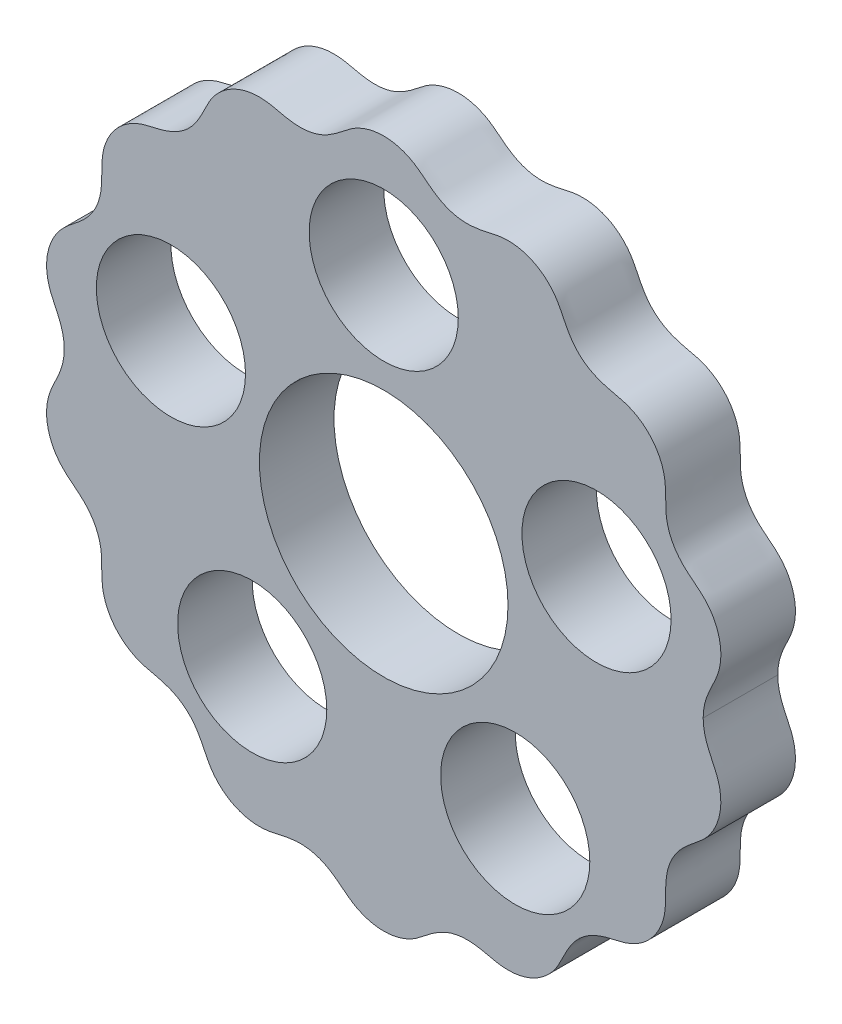
SolidWorks part; units mm, degrees
ref_plane "前视基准面" through (0, 0, 0) normal (0, 0, 1) x (1, 0, 0)
ref_plane "上视基准面" through (0, 0, 0) normal (0, 1, 0) x (1, 0, 0)
ref_plane "右视基准面" through (0, 0, 0) normal (1, 0, 0) x (0, 0, -1)
sketch "草图1" plane through (0, 0, 0) normal (0, 0, 1) x (1, 0, 0)
  line L0 (0, 0) -> (19.2125, 0) construction
  line L1 (19.2125, 0) -> (0, 0) construction
  line L2 (-13.0001, 0) -> (-15.8633, 0) construction
  spline S0 degree 4 poles (11.5135, 6.3336) (11.527, 6.2231) (11.5668, 6.0038) (11.6783, 5.6586) (11.9398, 5.2291) (12.3169, 4.8533) (12.7144, 4.5714) (13.0267, 4.2874) (13.2395, 4.0257) (13.3758, 3.817) (13.483, 3.611) (13.5552, 3.4371) (13.6059, 3.284) (13.6447, 3.1396) (13.6735, 3.0054) (13.6932, 2.8739) (13.7052, 2.751) (13.7102, 2.6455) (13.7111, 2.5545) (13.7091, 2.4602) (13.7056, 2.4011) (13.6985, 2.3206) (13.6885, 2.2338) (13.6763, 2.1514) (13.6589, 2.0606) (13.6342, 1.9553) (13.6051, 1.8508) (13.5717, 1.748) (13.517, 1.5994) (13.4338, 1.4076) (13.3178, 1.1764) (13.1849, 0.8966) (13.0721, 0.5847) (12.9994, 0.2368) (12.988, -0.1793) (13.0767, -0.6516) (13.2789, -1.1115) (13.526, -1.5754) (13.7034, -2.1387) (13.7437, -2.788) (13.6035, -3.4164) (13.3056, -3.968) (12.9261, -4.3975) (12.5717, -4.6706) (12.2507, -4.9214) (11.9118, -5.2776) (11.6864, -5.6334) (11.5501, -6.0331) (11.4958, -6.4466) (11.4872, -6.741) (11.4935, -7.0742) (11.4831, -7.4477) (11.3954, -7.9388) (11.1486, -8.5104) (10.7515, -9.0022) (10.2357, -9.3664) (9.7027, -9.5815) (9.1958, -9.6812) (8.6166, -9.8223) (8.0718, -10.1348) (7.6495, -10.5997) (7.3862, -11.1344) (7.1745, -11.6057) (6.843, -12.0753) (6.3712, -12.4934) (5.7973, -12.7698) (5.1733, -12.8799) (4.6659, -12.8482) (4.2925, -12.7678) (3.8977, -12.671) (3.4202, -12.5933) (2.9279, -12.6301) (2.4661, -12.8002) (2.1107, -13.0186) (1.8754, -13.1972) (1.6194, -13.4097) (1.3216, -13.6307) (0.885, -13.8635) (0.2879, -14.0232) (-0.3414, -14.0176) (-0.9463, -13.8403) (-1.4461, -13.5566) (-1.8397, -13.2219) (-2.312, -12.858) (-2.8966, -12.6285) (-3.5234, -12.5899) (-4.1054, -12.7185) (-4.6059, -12.8462) (-5.1801, -12.8785) (-5.7997, -12.769) (-6.3719, -12.4926) (-6.8429, -12.0754) (-7.1745, -11.6056) (-7.3862, -11.1344) (-7.6495, -10.5997) (-8.0718, -10.1348) (-8.6166, -9.8224) (-9.1958, -9.6811) (-9.7027, -9.5816) (-10.2356, -9.3663) (-10.6857, -9.0488) (-11.0496, -8.6352) (-11.2927, -8.1828) (-11.4194, -7.7999) (-11.4803, -7.4348) (-11.4944, -7.0969) (-11.4854, -6.7168) (-11.5007, -6.2924) (-11.604, -5.8312) (-11.8377, -5.3687) (-12.1451, -5.0141) (-12.4683, -4.7498) (-12.7596, -4.5257) (-12.997, -4.3126) (-13.2302, -4.0471) (-13.4408, -3.7207) (-13.641, -3.2535) (-13.7387, -2.7051) (-13.7032, -2.1387) (-13.526, -1.5754) (-13.2789, -1.1115) (-13.0767, -0.6516) (-12.988, -0.1793) (-12.9994, 0.2368) (-13.072, 0.5848) (-13.1849, 0.8966) (-13.3178, 1.1764) (-13.4338, 1.4076) (-13.517, 1.5994) (-13.5717, 1.748) (-13.6051, 1.8508) (-13.6342, 1.9553) (-13.6589, 2.0606) (-13.6763, 2.1514) (-13.6885, 2.2338) (-13.6985, 2.3206) (-13.7056, 2.4011) (-13.7091, 2.4602) (-13.7111, 2.5545) (-13.7102, 2.6455) (-13.7052, 2.751) (-13.6932, 2.8739) (-13.6735, 3.0054) (-13.6447, 3.1396) (-13.6059, 3.284) (-13.5552, 3.4371) (-13.483, 3.611) (-13.3758, 3.817) (-13.2395, 4.0257) (-13.0267, 4.2874) (-12.7144, 4.5714) (-12.3169, 4.8533) (-11.9398, 5.2291) (-11.6783, 5.6586) (-11.5668, 6.0038) (-11.527, 6.2231) (-11.5135, 6.3336) knots 0 0 0 0 0 0.007437 0.014874 0.024076 0.033277 0.042729 0.047455 0.052181 0.055773 0.059366 0.062958 0.064755 0.066551 0.069353 0.072156 0.073557 0.074958 0.076359 0.077761 0.079568 0.080471 0.081375 0.083182 0.08499 0.086797 0.088604 0.090412 0.092219 0.097388 0.102556 0.107725 0.112894 0.11954 0.126185 0.135429 0.144674 0.152994 0.161315 0.174598 0.187704 0.195264 0.202824 0.212649 0.217562 0.222474 0.235597 0.240509 0.245422 0.250335 0.255248 0.262808 0.270368 0.283474 0.29646 0.304321 0.312183 0.321594 0.331004 0.344001 0.353412 0.362824 0.370685 0.378547 0.391533 0.404567 0.412523 0.420479 0.425284 0.430089 0.439698 0.452744 0.457676 0.462607 0.467539 0.47247 0.479922 0.487374 0.500409 0.513394 0.521256 0.529118 0.538528 0.547939 0.560935 0.570347 0.579758 0.58762 0.595482 0.608467 0.621453 0.629315 0.637176 0.646588 0.655999 0.668996 0.678406 0.687817 0.695679 0.70354 0.716526 0.724297 0.732069 0.737708 0.743347 0.748986 0.754625 0.763148 0.771671 0.78029 0.788909 0.794231 0.799552 0.804873 0.810195 0.817798 0.825402 0.838685 0.847006 0.855326 0.864571 0.873815 0.88046 0.887106 0.892275 0.897444 0.902612 0.907781 0.909588 0.911396 0.913203 0.91501 0.916818 0.918625 0.919529 0.920432 0.922239 0.923641 0.925042 0.926443 0.927844 0.930647 0.933449 0.935245 0.937042 0.940634 0.944227 0.947819 0.952545 0.957271 0.966723 0.975924 0.985126 0.992563 1 1 1 1 1 construction
  spline S1 degree 4 poles (13.0001, 0) (13.0001, -0.0846) (13.0122, -0.3074) (13.0826, -0.6652) (13.2789, -1.1115) (13.526, -1.5754) (13.7034, -2.1387) (13.7437, -2.788) (13.6035, -3.4164) (13.3056, -3.968) (12.9261, -4.3975) (12.5717, -4.6706) (12.2507, -4.9214) (11.9118, -5.2776) (11.6864, -5.6334) (11.5501, -6.0331) (11.4958, -6.4466) (11.4872, -6.741) (11.4935, -7.0742) (11.4831, -7.4477) (11.3954, -7.9388) (11.1486, -8.5104) (10.7515, -9.0022) (10.2357, -9.3664) (9.7027, -9.5815) (9.1958, -9.6812) (8.6166, -9.8223) (8.0718, -10.1348) (7.6495, -10.5997) (7.3862, -11.1344) (7.1745, -11.6057) (6.843, -12.0753) (6.3712, -12.4934) (5.7973, -12.7698) (5.1733, -12.8799) (4.6659, -12.8482) (4.2925, -12.7678) (3.8977, -12.671) (3.4202, -12.5933) (2.9279, -12.6301) (2.4661, -12.8002) (2.1107, -13.0186) (1.8754, -13.1972) (1.6194, -13.4097) (1.3216, -13.6307) (0.885, -13.8635) (0.2879, -14.0232) (-0.3414, -14.0176) (-0.9463, -13.8403) (-1.4461, -13.5566) (-1.8397, -13.2219) (-2.312, -12.858) (-2.8966, -12.6285) (-3.5234, -12.5899) (-4.1054, -12.7185) (-4.6059, -12.8462) (-5.1801, -12.8785) (-5.7997, -12.769) (-6.3719, -12.4926) (-6.8429, -12.0754) (-7.1745, -11.6056) (-7.3862, -11.1344) (-7.6495, -10.5997) (-8.0718, -10.1348) (-8.6166, -9.8224) (-9.1958, -9.6811) (-9.7027, -9.5816) (-10.2356, -9.3663) (-10.6857, -9.0488) (-11.0496, -8.6352) (-11.2927, -8.1828) (-11.4194, -7.7999) (-11.4803, -7.4348) (-11.4944, -7.0969) (-11.4854, -6.7168) (-11.5007, -6.2924) (-11.604, -5.8312) (-11.8377, -5.3687) (-12.1451, -5.0141) (-12.4683, -4.7498) (-12.7596, -4.5257) (-12.997, -4.3126) (-13.2302, -4.0471) (-13.4408, -3.7207) (-13.641, -3.2535) (-13.7387, -2.7051) (-13.7032, -2.1387) (-13.526, -1.5754) (-13.2789, -1.1115) (-13.0827, -0.6652) (-13.0122, -0.3074) (-13.0001, -0.0846) (-13.0001, 0) knots 0.120529 0.120529 0.120529 0.120529 0.120529 0.126185 0.135429 0.144674 0.152994 0.161315 0.174598 0.187704 0.195264 0.202824 0.212649 0.217562 0.222474 0.235597 0.240509 0.245422 0.250335 0.255248 0.262808 0.270368 0.283474 0.29646 0.304321 0.312183 0.321594 0.331004 0.344001 0.353412 0.362824 0.370685 0.378547 0.391533 0.404567 0.412523 0.420479 0.425284 0.430089 0.439698 0.452744 0.457676 0.462607 0.467539 0.47247 0.479922 0.487374 0.500409 0.513394 0.521256 0.529118 0.538528 0.547939 0.560935 0.570347 0.579758 0.58762 0.595482 0.608467 0.621453 0.629315 0.637176 0.646588 0.655999 0.668996 0.678406 0.687817 0.695679 0.70354 0.716526 0.724297 0.732069 0.737708 0.743347 0.748986 0.754625 0.763148 0.771671 0.78029 0.788909 0.794231 0.799552 0.804873 0.810195 0.817798 0.825402 0.838685 0.847006 0.855326 0.864571 0.873815 0.879471 0.879471 0.879471 0.879471 0.879471
  spline S2 degree 4 poles (13.0001, 0) (13.0001, 0.0846) (13.0122, 0.3074) (13.0826, 0.6652) (13.2789, 1.1115) (13.526, 1.5754) (13.7034, 2.1387) (13.7437, 2.788) (13.6035, 3.4164) (13.3056, 3.968) (12.9261, 4.3975) (12.5717, 4.6706) (12.2507, 4.9214) (11.9118, 5.2776) (11.6864, 5.6334) (11.5501, 6.0331) (11.4958, 6.4466) (11.4872, 6.741) (11.4935, 7.0742) (11.4831, 7.4477) (11.3954, 7.9388) (11.1486, 8.5104) (10.7515, 9.0022) (10.2357, 9.3664) (9.7027, 9.5815) (9.1958, 9.6812) (8.6166, 9.8223) (8.0718, 10.1348) (7.6495, 10.5997) (7.3862, 11.1344) (7.1745, 11.6057) (6.843, 12.0753) (6.3712, 12.4934) (5.7973, 12.7698) (5.1733, 12.8799) (4.6659, 12.8482) (4.2925, 12.7678) (3.8977, 12.671) (3.4202, 12.5933) (2.9279, 12.6301) (2.4661, 12.8002) (2.1107, 13.0186) (1.8754, 13.1972) (1.6194, 13.4097) (1.3216, 13.6307) (0.885, 13.8635) (0.2879, 14.0232) (-0.3414, 14.0176) (-0.9463, 13.8403) (-1.4461, 13.5566) (-1.8397, 13.2219) (-2.312, 12.858) (-2.8966, 12.6285) (-3.5234, 12.5899) (-4.1054, 12.7185) (-4.6059, 12.8462) (-5.1801, 12.8785) (-5.7997, 12.769) (-6.3719, 12.4926) (-6.8429, 12.0754) (-7.1745, 11.6056) (-7.3862, 11.1344) (-7.6495, 10.5997) (-8.0718, 10.1348) (-8.6166, 9.8224) (-9.1958, 9.6811) (-9.7027, 9.5816) (-10.2356, 9.3663) (-10.6857, 9.0488) (-11.0496, 8.6352) (-11.2927, 8.1828) (-11.4194, 7.7999) (-11.4803, 7.4348) (-11.4944, 7.0969) (-11.4854, 6.7168) (-11.5007, 6.2924) (-11.604, 5.8312) (-11.8377, 5.3687) (-12.1451, 5.0141) (-12.4683, 4.7498) (-12.7596, 4.5257) (-12.997, 4.3126) (-13.2302, 4.0471) (-13.4408, 3.7207) (-13.641, 3.2535) (-13.7387, 2.7051) (-13.7032, 2.1387) (-13.526, 1.5754) (-13.2789, 1.1115) (-13.0827, 0.6652) (-13.0122, 0.3074) (-13.0001, 0.0846) (-13.0001, 0) knots 0.120529 0.120529 0.120529 0.120529 0.120529 0.126185 0.135429 0.144674 0.152994 0.161315 0.174598 0.187704 0.195264 0.202824 0.212649 0.217562 0.222474 0.235597 0.240509 0.245422 0.250335 0.255248 0.262808 0.270368 0.283474 0.29646 0.304321 0.312183 0.321594 0.331004 0.344001 0.353412 0.362824 0.370685 0.378547 0.391533 0.404567 0.412523 0.420479 0.425284 0.430089 0.439698 0.452744 0.457676 0.462607 0.467539 0.47247 0.479922 0.487374 0.500409 0.513394 0.521256 0.529118 0.538528 0.547939 0.560935 0.570347 0.579758 0.58762 0.595482 0.608467 0.621453 0.629315 0.637176 0.646588 0.655999 0.668996 0.678406 0.687817 0.695679 0.70354 0.716526 0.724297 0.732069 0.737708 0.743347 0.748986 0.754625 0.763148 0.771671 0.78029 0.788909 0.794231 0.799552 0.804873 0.810195 0.817798 0.825402 0.838685 0.847006 0.855326 0.864571 0.873815 0.879471 0.879471 0.879471 0.879471 0.879471
extrude "凸台-拉伸1" add sketch "草图1" along normal blind 3
sketch "草图2" plane through (0, 0, 3) normal (0, 0, 1) x (1, 0, 0)
  circle A0 centre (0, 0) radius 5
extrude "切除-拉伸1" cut sketch "草图2" against normal blind 8
sketch "草图3" plane through (0, 0, 3) normal (0, 0, 1) x (1, 0, 0)
  circle A0 centre (0, 9) radius 3
  circle A1 centre (8.5595, 2.7812) radius 3
  circle A2 centre (5.2901, -7.2812) radius 3
  circle A3 centre (-5.2901, -7.2812) radius 3
  circle A4 centre (-8.5595, 2.7812) radius 3
  point P15 (0, 0)
  dimension "D1" = 5
extrude "切除-拉伸2" cut sketch "草图3" against normal blind 3
sketch "草图4" plane through (0, 0, 3) normal (0, 0, 1) x (1, 0, 0)
  spline S0 degree 1 poles (-12.8501, 0) (12.8501, 0) knots 0 0 1 1 construction
  spline S1 degree 1 poles (12.8501, 0) (-12.8501, 0) knots 0 0 1 1 construction
  spline S2 degree 4 poles (-2818.5331, -2824.7068) (154.5376, 166.8472) (34.8169, -20.8637) (10.4629, -5.292) (13.2789, 1.1115) (13.526, 1.5754) (13.7034, 2.1387) (13.7437, 2.788) (13.6035, 3.4164) (13.3056, 3.968) (12.9261, 4.3975) (12.5717, 4.6706) (12.2507, 4.9214) (11.9118, 5.2776) (11.6864, 5.6334) (11.5501, 6.0331) (11.4958, 6.4466) (11.4872, 6.741) (11.4935, 7.0742) (11.4831, 7.4477) (11.3954, 7.9388) (11.1486, 8.5104) (10.7515, 9.0022) (10.2357, 9.3664) (9.7027, 9.5815) (9.1958, 9.6812) (8.6166, 9.8223) (8.0718, 10.1348) (7.6495, 10.5997) (7.3862, 11.1344) (7.1745, 11.6057) (6.843, 12.0753) (6.3712, 12.4934) (5.7973, 12.7698) (5.1733, 12.8799) (4.6659, 12.8482) (4.2925, 12.7678) (3.8977, 12.671) (3.4202, 12.5933) (2.9279, 12.6301) (2.4661, 12.8002) (2.1107, 13.0186) (1.8754, 13.1972) (1.6194, 13.4097) (1.3216, 13.6307) (0.885, 13.8635) (0.2879, 14.0232) (-0.3414, 14.0176) (-0.9463, 13.8403) (-1.4461, 13.5566) (-1.8397, 13.2219) (-2.312, 12.858) (-2.8966, 12.6285) (-3.5234, 12.5899) (-4.1054, 12.7185) (-4.6059, 12.8462) (-5.1801, 12.8785) (-5.7997, 12.769) (-6.3719, 12.4926) (-6.8429, 12.0754) (-7.1745, 11.6056) (-7.3862, 11.1344) (-7.6495, 10.5997) (-8.0718, 10.1348) (-8.6166, 9.8224) (-9.1958, 9.6811) (-9.7027, 9.5816) (-10.2356, 9.3663) (-10.6857, 9.0488) (-11.0496, 8.6352) (-11.2927, 8.1828) (-11.4194, 7.7999) (-11.4803, 7.4348) (-11.4944, 7.0969) (-11.4854, 6.7168) (-11.5007, 6.2924) (-11.604, 5.8312) (-11.8377, 5.3687) (-12.1451, 5.0141) (-12.4683, 4.7498) (-12.7596, 4.5257) (-12.997, 4.3126) (-13.2302, 4.0471) (-13.4408, 3.7207) (-13.641, 3.2535) (-13.7387, 2.7051) (-13.7032, 2.1387) (-13.526, 1.5754) (-13.2789, 1.1115) (-10.4939, -5.2237) (-34.2626, -20.5439) (-152.0911, 161.4116) (2865.9169, -2776.3995) knots -0.312826 -0.312826 -0.312826 -0.312826 -0.312826 0.126185 0.135429 0.144674 0.152994 0.161315 0.174598 0.187704 0.195264 0.202824 0.212649 0.217562 0.222474 0.235597 0.240509 0.245422 0.250335 0.255248 0.262808 0.270368 0.283474 0.29646 0.304321 0.312183 0.321594 0.331004 0.344001 0.353412 0.362824 0.370685 0.378547 0.391533 0.404567 0.412523 0.420479 0.425284 0.430089 0.439698 0.452744 0.457676 0.462607 0.467539 0.47247 0.479922 0.487374 0.500409 0.513394 0.521256 0.529118 0.538528 0.547939 0.560935 0.570347 0.579758 0.58762 0.595482 0.608467 0.621453 0.629315 0.637176 0.646588 0.655999 0.668996 0.678406 0.687817 0.695679 0.70354 0.716526 0.724297 0.732069 0.737708 0.743347 0.748986 0.754625 0.763148 0.771671 0.78029 0.788909 0.794231 0.799552 0.804873 0.810195 0.817798 0.825402 0.838685 0.847006 0.855326 0.864571 0.873815 1.307891 1.307891 1.307891 1.307891 1.307891 only from (13.0001, 0) to (-13.0001, 0)
  spline S3 degree 4 poles (2865.8022, 2776.2878) (-152.0878, -161.4065) (-34.2622, 20.5437) (-10.494, 5.2236) (-13.2789, -1.1115) (-13.526, -1.5754) (-13.7032, -2.1387) (-13.7387, -2.7051) (-13.641, -3.2535) (-13.4408, -3.7207) (-13.2302, -4.0471) (-12.997, -4.3126) (-12.7596, -4.5257) (-12.4683, -4.7498) (-12.1451, -5.0141) (-11.8377, -5.3687) (-11.604, -5.8312) (-11.5007, -6.2924) (-11.4854, -6.7168) (-11.4944, -7.0969) (-11.4803, -7.4348) (-11.4194, -7.7999) (-11.2927, -8.1828) (-11.0496, -8.6352) (-10.6857, -9.0488) (-10.2356, -9.3663) (-9.7027, -9.5816) (-9.1958, -9.6811) (-8.6166, -9.8224) (-8.0718, -10.1348) (-7.6495, -10.5997) (-7.3862, -11.1344) (-7.1745, -11.6056) (-6.8429, -12.0754) (-6.3719, -12.4926) (-5.7997, -12.769) (-5.1801, -12.8785) (-4.6059, -12.8462) (-4.1054, -12.7185) (-3.5234, -12.5899) (-2.8966, -12.6285) (-2.312, -12.858) (-1.8397, -13.2219) (-1.4461, -13.5566) (-0.9463, -13.8403) (-0.3414, -14.0176) (0.2879, -14.0232) (0.885, -13.8635) (1.3216, -13.6307) (1.6194, -13.4097) (1.8754, -13.1972) (2.1107, -13.0186) (2.4661, -12.8002) (2.9279, -12.6301) (3.4202, -12.5933) (3.8977, -12.671) (4.2925, -12.7678) (4.6659, -12.8482) (5.1733, -12.8799) (5.7973, -12.7698) (6.3712, -12.4934) (6.843, -12.0753) (7.1745, -11.6057) (7.3862, -11.1344) (7.6495, -10.5997) (8.0718, -10.1348) (8.6166, -9.8223) (9.1958, -9.6812) (9.7027, -9.5815) (10.2357, -9.3664) (10.7515, -9.0022) (11.1486, -8.5104) (11.3954, -7.9388) (11.4831, -7.4477) (11.4935, -7.0742) (11.4872, -6.741) (11.4958, -6.4466) (11.5501, -6.0331) (11.6864, -5.6334) (11.9118, -5.2776) (12.2507, -4.9214) (12.5717, -4.6706) (12.9261, -4.3975) (13.3056, -3.968) (13.6035, -3.4164) (13.7437, -2.788) (13.7034, -2.1387) (13.526, -1.5754) (13.2789, -1.1115) (10.463, 5.292) (34.8162, 20.8633) (154.5321, -166.8385) (-2818.3451, 2824.5177) knots -0.307887 -0.307887 -0.307887 -0.307887 -0.307887 0.126185 0.135429 0.144674 0.152994 0.161315 0.174598 0.182202 0.189805 0.195127 0.200448 0.205769 0.211091 0.21971 0.228329 0.236852 0.245375 0.251014 0.256653 0.262292 0.267931 0.275703 0.283474 0.29646 0.304321 0.312183 0.321594 0.331004 0.344001 0.353412 0.362824 0.370685 0.378547 0.391533 0.404518 0.41238 0.420242 0.429653 0.439065 0.452061 0.461472 0.470882 0.478744 0.486606 0.499591 0.512626 0.520078 0.52753 0.532461 0.537393 0.542324 0.547256 0.560302 0.569911 0.574716 0.579521 0.587477 0.595433 0.608467 0.621453 0.629315 0.637176 0.646587 0.655999 0.668996 0.678406 0.687817 0.695679 0.70354 0.716526 0.729632 0.737192 0.744752 0.749665 0.754578 0.759491 0.764403 0.777526 0.782438 0.787351 0.797175 0.804736 0.812296 0.825402 0.838685 0.847006 0.855326 0.864571 0.873815 1.312819 1.312819 1.312819 1.312819 1.312819 only from (-13.0001, 0) to (13.0001, 0)
  spline S4 degree 4 poles (13.0001, 0) (13.0001, 0.0846) (13.0122, 0.3074) (13.0826, 0.6652) (13.2789, 1.1115) (13.526, 1.5754) (13.7034, 2.1387) (13.7437, 2.788) (13.6035, 3.4164) (13.3056, 3.968) (12.9261, 4.3975) (12.5717, 4.6706) (12.2507, 4.9214) (11.9118, 5.2776) (11.6864, 5.6334) (11.5501, 6.0331) (11.4958, 6.4466) (11.4872, 6.741) (11.4935, 7.0742) (11.4831, 7.4477) (11.3954, 7.9388) (11.1486, 8.5104) (10.7515, 9.0022) (10.2357, 9.3664) (9.7027, 9.5815) (9.1958, 9.6812) (8.6166, 9.8223) (8.0718, 10.1348) (7.6495, 10.5997) (7.3862, 11.1344) (7.1745, 11.6057) (6.843, 12.0753) (6.3712, 12.4934) (5.7973, 12.7698) (5.1733, 12.8799) (4.6659, 12.8482) (4.2925, 12.7678) (3.8977, 12.671) (3.4202, 12.5933) (2.9279, 12.6301) (2.4661, 12.8002) (2.1107, 13.0186) (1.8754, 13.1972) (1.6194, 13.4097) (1.3216, 13.6307) (0.885, 13.8635) (0.2879, 14.0232) (-0.3414, 14.0176) (-0.9463, 13.8403) (-1.4461, 13.5566) (-1.8397, 13.2219) (-2.312, 12.858) (-2.8966, 12.6285) (-3.5234, 12.5899) (-4.1054, 12.7185) (-4.6059, 12.8462) (-5.1801, 12.8785) (-5.7997, 12.769) (-6.3719, 12.4926) (-6.8429, 12.0754) (-7.1745, 11.6056) (-7.3862, 11.1344) (-7.6495, 10.5997) (-8.0718, 10.1348) (-8.6166, 9.8224) (-9.1958, 9.6811) (-9.7027, 9.5816) (-10.2356, 9.3663) (-10.6857, 9.0488) (-11.0496, 8.6352) (-11.2927, 8.1828) (-11.4194, 7.7999) (-11.4803, 7.4348) (-11.4944, 7.0969) (-11.4854, 6.7168) (-11.5007, 6.2924) (-11.604, 5.8312) (-11.8377, 5.3687) (-12.1451, 5.0141) (-12.4683, 4.7498) (-12.7596, 4.5257) (-12.997, 4.3126) (-13.2302, 4.0471) (-13.4408, 3.7207) (-13.641, 3.2535) (-13.7387, 2.7051) (-13.7032, 2.1387) (-13.526, 1.5754) (-13.2789, 1.1115) (-13.0827, 0.6652) (-13.0122, 0.3074) (-13.0001, 0.0846) (-13.0001, 0) knots 0.120529 0.120529 0.120529 0.120529 0.120529 0.126185 0.135429 0.144674 0.152994 0.161315 0.174598 0.187704 0.195264 0.202824 0.212649 0.217562 0.222474 0.235597 0.240509 0.245422 0.250335 0.255248 0.262808 0.270368 0.283474 0.29646 0.304321 0.312183 0.321594 0.331004 0.344001 0.353412 0.362824 0.370685 0.378547 0.391533 0.404567 0.412523 0.420479 0.425284 0.430089 0.439698 0.452744 0.457676 0.462607 0.467539 0.47247 0.479922 0.487374 0.500409 0.513394 0.521256 0.529118 0.538528 0.547939 0.560935 0.570347 0.579758 0.58762 0.595482 0.608467 0.621453 0.629315 0.637176 0.646588 0.655999 0.668996 0.678406 0.687817 0.695679 0.70354 0.716526 0.724297 0.732069 0.737708 0.743347 0.748986 0.754625 0.763148 0.771671 0.78029 0.788909 0.794231 0.799552 0.804873 0.810195 0.817798 0.825402 0.838685 0.847006 0.855326 0.864571 0.873815 0.879471 0.879471 0.879471 0.879471 0.879471
  spline S5 degree 4 poles (-13.0001, 0) (-13.0001, -0.0846) (-13.0122, -0.3074) (-13.0827, -0.6652) (-13.2789, -1.1115) (-13.526, -1.5754) (-13.7032, -2.1387) (-13.7387, -2.7051) (-13.641, -3.2535) (-13.4408, -3.7207) (-13.2302, -4.0471) (-12.997, -4.3126) (-12.7596, -4.5257) (-12.4683, -4.7498) (-12.1451, -5.0141) (-11.8377, -5.3687) (-11.604, -5.8312) (-11.5007, -6.2924) (-11.4854, -6.7168) (-11.4944, -7.0969) (-11.4803, -7.4348) (-11.4194, -7.7999) (-11.2927, -8.1828) (-11.0496, -8.6352) (-10.6857, -9.0488) (-10.2356, -9.3663) (-9.7027, -9.5816) (-9.1958, -9.6811) (-8.6166, -9.8224) (-8.0718, -10.1348) (-7.6495, -10.5997) (-7.3862, -11.1344) (-7.1745, -11.6056) (-6.8429, -12.0754) (-6.3719, -12.4926) (-5.7997, -12.769) (-5.1801, -12.8785) (-4.6059, -12.8462) (-4.1054, -12.7185) (-3.5234, -12.5899) (-2.8966, -12.6285) (-2.312, -12.858) (-1.8397, -13.2219) (-1.4461, -13.5566) (-0.9463, -13.8403) (-0.3414, -14.0176) (0.2879, -14.0232) (0.885, -13.8635) (1.3216, -13.6307) (1.6194, -13.4097) (1.8754, -13.1972) (2.1107, -13.0186) (2.4661, -12.8002) (2.9279, -12.6301) (3.4202, -12.5933) (3.8977, -12.671) (4.2925, -12.7678) (4.6659, -12.8482) (5.1733, -12.8799) (5.7973, -12.7698) (6.3712, -12.4934) (6.843, -12.0753) (7.1745, -11.6057) (7.3862, -11.1344) (7.6495, -10.5997) (8.0718, -10.1348) (8.6166, -9.8223) (9.1958, -9.6812) (9.7027, -9.5815) (10.2357, -9.3664) (10.7515, -9.0022) (11.1486, -8.5104) (11.3954, -7.9388) (11.4831, -7.4477) (11.4935, -7.0742) (11.4872, -6.741) (11.4958, -6.4466) (11.5501, -6.0331) (11.6864, -5.6334) (11.9118, -5.2776) (12.2507, -4.9214) (12.5717, -4.6706) (12.9261, -4.3975) (13.3056, -3.968) (13.6035, -3.4164) (13.7437, -2.788) (13.7034, -2.1387) (13.526, -1.5754) (13.2789, -1.1115) (13.0826, -0.6652) (13.0122, -0.3074) (13.0001, -0.0846) (13.0001, 0) knots 0.120529 0.120529 0.120529 0.120529 0.120529 0.126185 0.135429 0.144674 0.152994 0.161315 0.174598 0.182202 0.189805 0.195127 0.200448 0.205769 0.211091 0.21971 0.228329 0.236852 0.245375 0.251014 0.256653 0.262292 0.267931 0.275703 0.283474 0.29646 0.304321 0.312183 0.321594 0.331004 0.344001 0.353412 0.362824 0.370685 0.378547 0.391533 0.404518 0.41238 0.420242 0.429653 0.439065 0.452061 0.461472 0.470882 0.478744 0.486606 0.499591 0.512626 0.520078 0.52753 0.532461 0.537393 0.542324 0.547256 0.560302 0.569911 0.574716 0.579521 0.587477 0.595433 0.608467 0.621453 0.629315 0.637176 0.646587 0.655999 0.668996 0.678406 0.687817 0.695679 0.70354 0.716526 0.729632 0.737192 0.744752 0.749665 0.754578 0.759491 0.764403 0.777526 0.782438 0.787351 0.797175 0.804736 0.812296 0.825402 0.838685 0.847006 0.855326 0.864571 0.873815 0.879471 0.879471 0.879471 0.879471 0.879471
  spline S6 degree 3 poles (-12.8501, 0) (-12.8502, -0.2515) (-12.94, -0.7631) (-13.2805, -1.4167) (-13.5334, -2.0348) (-13.6076, -2.9315) (-13.2934, -3.8053) (-12.6605, -4.4301) (-12.0701, -4.8537) (-11.5877, -5.4568) (-11.3411, -6.1911) (-11.3427, -6.9391) (-11.3249, -7.8359) (-10.9033, -8.6615) (-10.1991, -9.2211) (-9.5799, -9.4656) (-8.8743, -9.5842) (-8.1645, -9.8812) (-7.5958, -10.4086) (-7.245, -11.0771) (-6.9596, -11.695) (-6.5083, -12.1943) (-5.9358, -12.5477) (-5.2846, -12.723) (-4.6172, -12.7053) (-3.9415, -12.5115) (-3.1794, -12.4338) (-2.4276, -12.6251) (-1.7979, -13.0528) (-1.2759, -13.5055) (-0.6664, -13.7851) (-0.0001, -13.8824) (0.6667, -13.7853) (1.2758, -13.5052) (1.7972, -13.0529) (2.428, -12.6252) (3.1792, -12.434) (3.942, -12.5109) (4.6166, -12.7054) (5.2846, -12.7232) (5.9359, -12.5475) (6.5083, -12.1944) (6.9597, -11.695) (7.2451, -11.0771) (7.5958, -10.4086) (8.1645, -9.8812) (8.8743, -9.5842) (9.5799, -9.4655) (10.1991, -9.2211) (10.9033, -8.6615) (11.3249, -7.836) (11.3428, -6.9391) (11.3411, -6.1911) (11.5877, -5.4568) (12.0701, -4.8535) (12.6602, -4.4297) (13.2935, -3.8056) (13.6075, -2.9314) (13.5335, -2.0349) (13.2805, -1.4167) (12.9401, -0.7631) (12.8502, -0.2515) (12.8501, 0) knots 0.120528 0.120528 0.120528 0.120528 0.132386 0.144245 0.156103 0.167962 0.191679 0.203537 0.215396 0.227254 0.239113 0.250971 0.26283 0.286547 0.298405 0.310264 0.322122 0.333981 0.345839 0.357698 0.369556 0.381415 0.393273 0.405132 0.41699 0.428849 0.440707 0.452566 0.464424 0.476283 0.488142 0.5 0.511859 0.523717 0.535576 0.547434 0.559293 0.571151 0.58301 0.594868 0.606727 0.618585 0.630444 0.642302 0.654161 0.666019 0.677878 0.689736 0.701595 0.713453 0.73717 0.749029 0.760887 0.772746 0.784604 0.796463 0.808321 0.832038 0.843897 0.855755 0.867614 0.879472 0.879472 0.879472 0.879472
  spline S7 degree 3 poles (12.8501, 0) (12.8502, 0.2515) (12.9401, 0.7631) (13.2805, 1.4167) (13.5335, 2.0349) (13.6075, 2.9314) (13.2935, 3.8056) (12.6602, 4.4297) (12.0701, 4.8535) (11.5877, 5.4568) (11.3411, 6.1911) (11.3428, 6.9391) (11.3249, 7.836) (10.9033, 8.6615) (10.1991, 9.2211) (9.5799, 9.4655) (8.8743, 9.5842) (8.1645, 9.8812) (7.5958, 10.4086) (7.2451, 11.0771) (6.9597, 11.695) (6.5083, 12.1944) (5.9359, 12.5475) (5.2846, 12.7232) (4.6166, 12.7054) (3.942, 12.5109) (3.1792, 12.434) (2.428, 12.6252) (1.7972, 13.0529) (1.2758, 13.5052) (0.6667, 13.7853) (-0.0001, 13.8824) (-0.6664, 13.7851) (-1.2759, 13.5055) (-1.7979, 13.0528) (-2.4276, 12.6251) (-3.1794, 12.4338) (-3.9415, 12.5115) (-4.6172, 12.7053) (-5.2846, 12.723) (-5.9358, 12.5477) (-6.5083, 12.1943) (-6.9596, 11.695) (-7.245, 11.0771) (-7.5958, 10.4086) (-8.1645, 9.8812) (-8.8743, 9.5842) (-9.5799, 9.4656) (-10.1991, 9.2211) (-10.9033, 8.6615) (-11.3249, 7.8359) (-11.3427, 6.9391) (-11.3411, 6.1911) (-11.5877, 5.4568) (-12.0701, 4.8537) (-12.6605, 4.4301) (-13.2934, 3.8053) (-13.6076, 2.9315) (-13.5334, 2.0348) (-13.2805, 1.4167) (-12.94, 0.7631) (-12.8502, 0.2515) (-12.8501, 0) knots 0.120528 0.120528 0.120528 0.120528 0.132386 0.144245 0.156103 0.167962 0.191679 0.203537 0.215396 0.227254 0.239113 0.250971 0.26283 0.286547 0.298405 0.310264 0.322122 0.333981 0.345839 0.357698 0.369556 0.381415 0.393273 0.405132 0.41699 0.428849 0.440707 0.452566 0.464424 0.476283 0.488141 0.5 0.511858 0.523717 0.535575 0.547434 0.559293 0.571151 0.58301 0.594868 0.606727 0.618585 0.630444 0.642302 0.654161 0.666019 0.677878 0.689736 0.701595 0.713453 0.73717 0.749029 0.760887 0.772746 0.784604 0.796463 0.808321 0.832038 0.843897 0.855755 0.867614 0.879472 0.879472 0.879472 0.879472
  dimension "D1" = 0
  dimension "D2" = 0.15
extrude "切除-拉伸3" cut sketch "草图4" against normal blind 10
